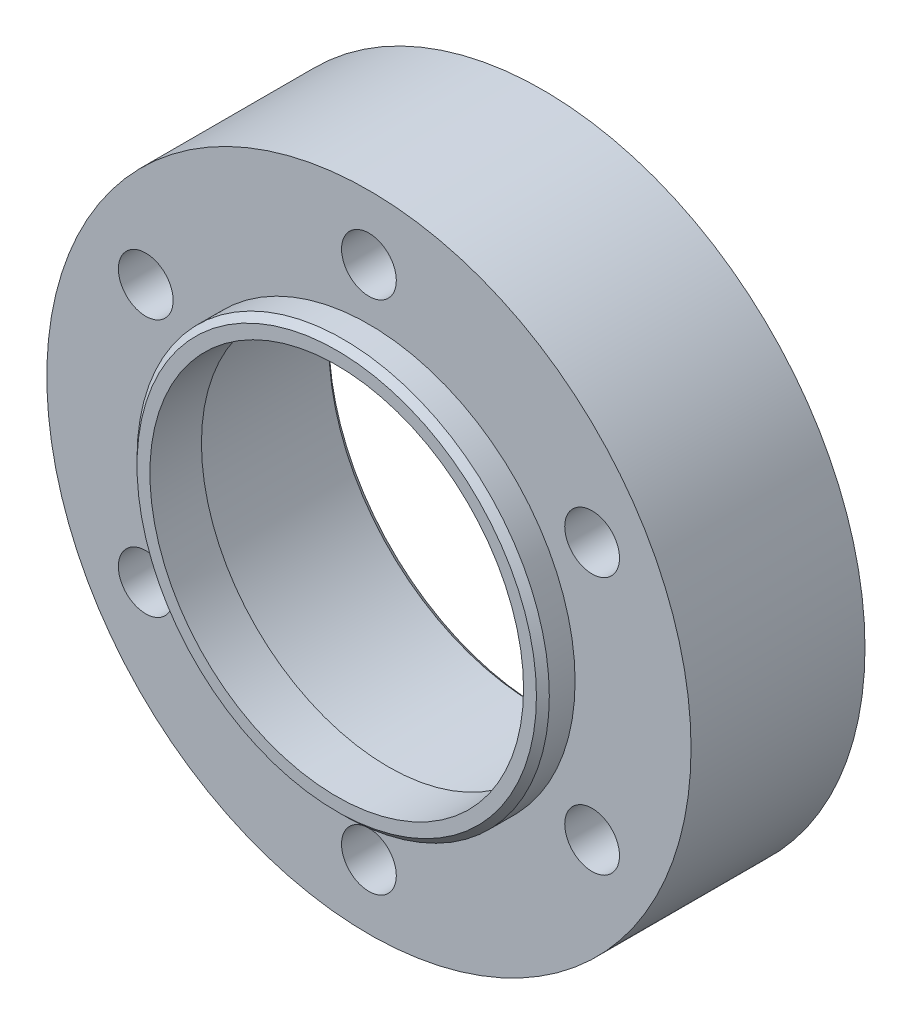
SolidWorks part; units mm, degrees
ref_plane "Plan de face" through (0, 0, 0) normal (0, 0, 1) x (1, 0, 0)
ref_plane "Plan de dessus" through (0, 0, 0) normal (0, 1, 0) x (1, 0, 0)
ref_plane "Plan de droite" through (0, 0, 0) normal (1, 0, 0) x (0, 0, -1)
sketch "Esquisse2" plane through (0, 0, 0) normal (0, 0, 1) x (1, 0, 0)
  circle A0 centre (0, 0) radius 50
  dimension "D1" = 100
extrude "Boss.-Extru.1" add sketch "Esquisse2" along normal blind 27
sketch "Esquisse3" plane through (0, 0, 0) normal (0, 0, -1) x (-1, 0, 0)
  circle A0 centre (0, 0) radius 32.2
  dimension "D1" = 64.4
extrude "Enlèv. mat.-Extru.1" cut sketch "Esquisse3" against normal blind 24
sketch "Esquisse4" plane through (0, 0, 27) normal (0, 0, 1) x (1, 0, 0)
  circle A0 centre (0, 0) radius 32
  dimension "D1" = 64
extrude "Boss.-Extru.2" add sketch "Esquisse4" along normal blind 5
sketch "Esquisse5" plane through (0, 0, 32) normal (0, 0, 1) x (1, 0, 0)
  circle A0 centre (0, 0) radius 29
  dimension "D1" = 58
extrude "Enlèv. mat.-Extru.2" cut sketch "Esquisse5" against normal through all
sketch "Esquisse6" plane through (0, 0, 0) normal (0, 0, -1) x (-1, 0, 0)
  circle A0 centre (0, 40) radius 4.25
  circle A1 centre (34.641, 20) radius 4.25
  circle A2 centre (34.641, -20) radius 4.25
  circle A3 centre (0, -40) radius 4.25
  circle A4 centre (-34.641, -20) radius 4.25
  circle A5 centre (-34.641, 20) radius 4.25
  point P16 (0, 0)
  dimension "D1" = 8.5
  dimension "D2" = 40
  dimension "D3" = 6
extrude "Enlèv. mat.-Extru.3" cut sketch "Esquisse6" against normal through all
chamfer "Chanfrein1" distance 1 angle 45 2 edges at (-32.2, 0, 0) (32, 0, 32)
